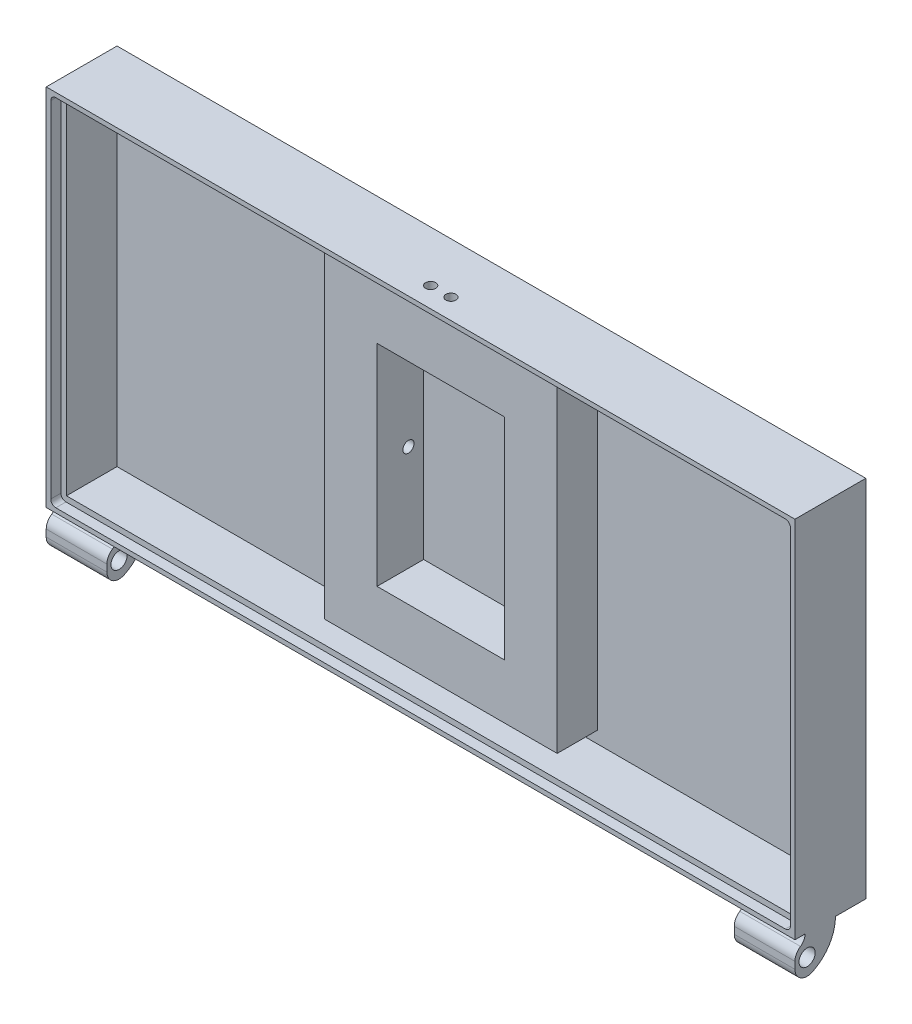
SolidWorks part; units mm, degrees
ref_plane "Front Plane" through (0, 0, 0) normal (0, 0, 1) x (1, 0, 0)
ref_plane "Top Plane" through (0, 0, 0) normal (0, 1, 0) x (1, 0, 0)
ref_plane "Right Plane" through (0, 0, 0) normal (1, 0, 0) x (0, 0, -1)
ref_plane "Plane1" through (0, 0, 35) normal (0, 0, 1) x (1, 0, 0)
sketch "Sketch1" plane through (0, 0, 35) normal (0, 0, 1) x (1, 0, 0)
  line L0 (370, 0) -> (370, 180)
  line L1 (370, 180) -> (0, 180)
  line L2 (0, 180) -> (0, 0)
  line L3 (0, 0) -> (370, 0)
extrude "Boss-Extrude1" add sketch "Sketch1" against normal blind 35
sketch "Sketch2" plane through (0, 0, 35) normal (0, 0, 1) x (1, 0, 0)
  line L0 (2.25, 177.75) -> (2.25, 2.25)
  line L1 (2.25, 2.25) -> (367.75, 2.25)
  line L2 (367.75, 2.25) -> (367.75, 177.75)
  line L3 (367.75, 177.75) -> (2.25, 177.75)
extrude "Cut-Extrude1" cut sketch "Sketch2" against normal blind 5
sketch "Sketch3" plane through (0, 0, 30) normal (0, 0, 1) x (1, 0, 0)
  line L0 (365, 5) -> (365, 175)
  line L1 (365, 175) -> (5, 175)
  line L2 (5, 175) -> (5, 5)
  line L3 (5, 5) -> (365, 5)
extrude "Cut-Extrude2" cut sketch "Sketch3" against normal blind 25
sketch "Sketch4" plane through (0, 5, 0) normal (0, 1, 0) x (-1, 0, 0)
  line L0 (-127.5, 25) -> (-127.5, 5)
  line L1 (-127.5, 5) -> (-242.5, 5)
  line L2 (-242.5, 5) -> (-242.5, 25)
  line L3 (-242.5, 25) -> (-127.5, 25)
extrude "Boss-Extrude2" add sketch "Sketch4" along normal blind 170
sketch "Sketch5" plane through (0, 0, 0) normal (0, 0, -1) x (-1, 0, 0)
  line L0 (-132.5, 16) -> (-132.5, 164)
  line L1 (-132.5, 164) -> (-237.5, 164)
  line L2 (-237.5, 164) -> (-237.5, 16)
  line L3 (-237.5, 16) -> (-132.5, 16)
extrude "Cut-Extrude3" cut sketch "Sketch5" against normal blind 18
sketch "Sketch6" plane through (0, 0, 18) normal (0, 0, -1) x (-1, 0, 0)
  line L0 (-148.5, 147) -> (-148.5, 33)
  line L1 (-148.5, 33) -> (-221.5, 33)
  line L2 (-221.5, 33) -> (-221.5, 147)
  line L3 (-221.5, 147) -> (-148.5, 147)
extrude "Boss-Extrude3" add sketch "Sketch6" along normal blind 18
hole_wizard "Ø15.0 (15) Diameter Hole1" positions "Sketch8" profile "Sketch7" hole size "Ø15.0" standard "ANSI Metric"
sketch "Sketch8" plane through (148.5, 0, 0) normal (-1, 0, 0) x (0, 0, 1)
  point P0 (9.5, 90)
sketch "Sketch7" plane through (148.5, 90, 9.5) normal (0, 1, 0) x (0, 0, 1)
  line L0 (0, 0) -> (0, 11)
  line L1 (0, 11) -> (2.75, 11)
  line L2 (2.75, 11) -> (2.75, 0)
  line L5 (2.75, 0) -> (0, 0)
  line L10 (0, 11) -> (-2.75, 11) construction
  line L11 (0, -6.35) -> (0, 107.95) construction
  dimension "Hole Dia." = 5.5
  dimension "Hole Depth" = 11
  dimension "Drill Angle" = 180
fillet "Fillet1" radius 2.5 4 edges at (2.25, 177.75, 32.5) (2.25, 2.25, 32.5) (367.75, 2.25, 32.5) (367.75, 177.75, 32.5)
fillet "Fillet2" radius 15 8 edges at (132.5, 16, 9) (237.5, 164, 9) (237.5, 16, 9) (221.5, 147, 9) (132.5, 164, 9) (148.5, 147, 9) (148.5, 33, 9) (221.5, 33, 9)
sketch "Sketch11" plane through (0, 0, 35) normal (0, 0, 1) x (1, 0, 0)
  line L0 (370, -5) -> (370, -20)
  line L1 (370, -20) -> (340, -20)
  line L2 (340, -20) -> (340, -5)
  line L4 (340, -5) -> (370, -5)
  line L5 (185, 29.3051) -> (185, -32.3354) construction
  line L6 (30, -20) -> (30, -5)
  line L7 (0, -20) -> (30, -20)
  line L8 (0, -5) -> (0, -20)
  line L9 (30, -5) -> (0, -5)
  line L10 (370, 0) -> (370, 180) construction
  line L11 (0, 0) -> (370, 0) construction
  dimension "D1" = 30
  dimension "D2" = 15
  dimension "D3" = 0
  dimension "D4" = 5
revolve "Revolve1" add sketch "Sketch11" angle 90 about axis through (0, 0, 35) along (1, 0, 0)
sketch "Sketch12" plane through (370, 0, 0) normal (1, 0, 0) x (0, 0, -1)
  circle A0 centre (-29, -10.5) radius 4
  dimension "D1" = 8
  dimension "D3" = 9.5
  dimension "D2" = 14
extrude "Cut-Extrude4" cut sketch "Sketch12" against normal through all
fillet "Fillet4" radius 6 2 edges at (15, -20, 35) (355, -20, 35)
fillet "Fillet5" radius 6 2 edges at (15, -5, 35) (355, -5, 35)
sketch "Sketch13" plane through (0, 0, 25) normal (0, 0, 1) x (1, 0, 0)
  line L1 (153.5, 142) -> (216.5, 142)
  line L2 (153.5, 142) -> (153.5, 38)
  line L3 (153.5, 38) -> (216.5, 38)
  line L4 (216.5, 142) -> (216.5, 38)
  line L6 (127.5, 5) -> (242.5, 5) construction
  line L8 (242.5, 175) -> (242.5, 5) construction
  dimension "D1" = 63
  dimension "D2" = 104
  dimension "D3" = 33
  dimension "D4" = 26
extrude "Cut-Extrude5" cut sketch "Sketch13" against normal blind 23
sketch "Sketch14" plane through (0, 0, 25) normal (0, 0, 1) x (1, 0, 0)
  line L0 (127.5, 175) -> (127.5, 5) construction
  line L1 (127.5, 169) -> (242.5, 169)
  line L2 (127.5, 169) -> (127.5, 175)
  line L3 (127.5, 175) -> (242.5, 175)
  line L4 (242.5, 169) -> (242.5, 175)
  dimension "D1" = 6
extrude "Cut-Extrude6" cut sketch "Sketch14" against normal up to vertex
sketch "Sketch15" plane through (0, 0, 25) normal (0, 0, 1) x (1, 0, 0)
  line L0 (5, 5) -> (365, 5) construction
  line L1 (127.5, 5) -> (242.5, 5)
  line L2 (127.5, 5) -> (127.5, 11)
  line L3 (127.5, 11) -> (242.5, 11)
  line L4 (242.5, 5) -> (242.5, 11)
  line L5 (127.5, 5) -> (242.5, 5) construction
  line L6 (242.5, 169) -> (242.5, 5) construction
  dimension "D1" = 6
  dimension "D2" = 115
extrude "Cut-Extrude7" cut sketch "Sketch15" against normal up to vertex
sketch "Sketch17" plane through (0, 180, 0) normal (0, 1, 0) x (1, 0, 0)
  line L0 (0, 0) -> (0, -35) construction
  line L1 (370, -35) -> (0, -35) construction
  circle A0 centre (180, -25) radius 2.5
  circle A1 centre (190, -25) radius 2.5
  dimension "D1" = 5
  dimension "D2" = 5
  dimension "D3" = 10
  dimension "D4" = 180
  dimension "D5" = 10
  dimension "D6" = 10
extrude "Cut-Extrude8" cut sketch "Sketch17" against normal up to next
sketch "Sketch18" plane through (221.5, 0, 0) normal (1, 0, 0) x (0, 0, -1)
  circle A0 centre (-9.5, 90) radius 2.75 construction
  circle A1 centre (-9.5, 90) radius 2.75
extrude "Cut-Extrude9" cut sketch "Sketch18" against normal blind 10
